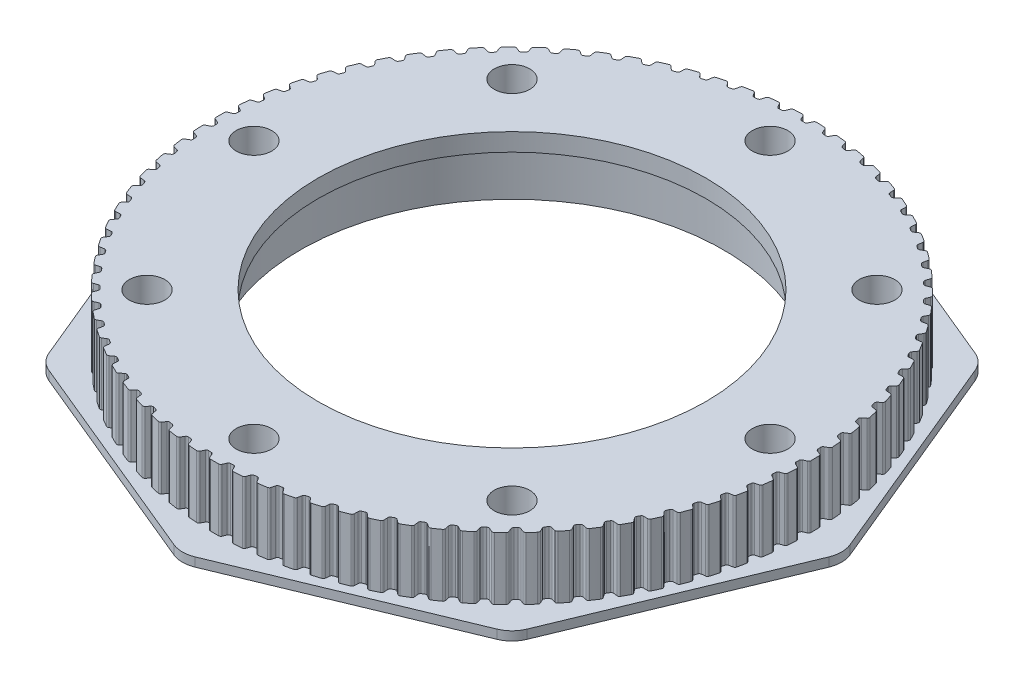
SolidWorks part; units mm, degrees
material "PVC rigide"
ref_plane "Plan de face" through (0, 0, 0) normal (0, 0, 1) x (1, 0, 0)
ref_plane "Plan de dessus" through (0, 0, 0) normal (0, 1, 0) x (1, 0, 0)
ref_plane "Plan de droite" through (0, 0, 0) normal (1, 0, 0) x (0, 0, -1)
sketch "Esquisse1" plane through (0, 0, 0) normal (0, 1, 0) x (1, 0, 0)
  line L0 (0, 0) -> (0, 74.5768) construction
  line L1 (-52.7338, 52.7338) -> (-74.5768, 0)
  line L2 (-74.5768, 0) -> (-52.7338, -52.7338)
  line L3 (-52.7338, -52.7338) -> (0, -74.5768)
  line L4 (0, -74.5768) -> (52.7338, -52.7338)
  line L5 (52.7338, -52.7338) -> (74.5768, 0)
  line L6 (74.5768, 0) -> (52.7338, 52.7338)
  line L7 (52.7338, 52.7338) -> (0, 74.5768)
  line L8 (0, 74.5768) -> (-52.7338, 52.7338)
  circle A1 centre (0, 0) radius 47.55
  circle A2 centre (0, 0) radius 68.9 construction
  dimension "D2" = 95.1
  dimension "D3" = 137.8
extrude "Boss.-Extru.1" add sketch "Esquisse1" along normal blind 16
fillet "Congé1" radius 6.2 8 edges at (0, 8, -74.5768) (52.7338, 8, -52.7338) (74.5768, 8, 0) (-52.7338, 8, 52.7338) (-74.5768, 8, 0) (-52.7338, 8, -52.7338) (52.7338, 8, 52.7338) (0, 8, 74.5768)
sketch "Esquisse2" plane through (0, 16, 0) normal (0, 1, 0) x (1, 0, 0)
  circle A0 centre (0, 0) radius 58 construction
  circle A1 centre (-58, 0) radius 3.1
  circle A2 centre (-41.0122, 41.0122) radius 3.1
  circle A3 centre (0, 58) radius 3.1
  circle A4 centre (41.0122, 41.0122) radius 3.1
  circle A5 centre (58, 0) radius 3.1
  circle A6 centre (41.0122, -41.0122) radius 3.1
  circle A7 centre (0, -58) radius 3.1
  circle A8 centre (-41.0122, -41.0122) radius 3.1
  dimension "D1" = 116
  dimension "D2" = 6.2
  dimension "D3" = 8
extrude "Enlèv. mat.-Extru.1" cut sketch "Esquisse2" against normal through all
sketch "Esquisse3" plane through (0, 16, 0) normal (0, 1, 0) x (1, 0, 0)
  circle A0 centre (-58, 0) radius 4
  circle A1 centre (-41.0122, 41.0122) radius 4
  circle A2 centre (0, 58) radius 4
  circle A3 centre (41.0122, 41.0122) radius 4
  circle A4 centre (58, 0) radius 4
  circle A5 centre (41.0122, -41.0122) radius 4
  circle A6 centre (0, -58) radius 4
  circle A7 centre (-41.0122, -41.0122) radius 4
  dimension "D1" = 8
  dimension "D2" = 8
extrude "Enlèv. mat.-Extru.2" cut sketch "Esquisse3" against normal blind 12.8
sketch "Esquisse5" plane through (0, 16, 0) normal (0, 1, 0) x (1, 0, 0)
  circle A0 centre (0, 0) radius 66.85
  dimension "D1" = 133.7
extrude "Enlèv. mat.-Extru.3" cut sketch "Esquisse5" against normal offset from surface (14 mm away) 2 flip side to cut up to face at (-58, 0, 3.1)
sketch "Esquisse6" plane through (0, 16, 0) normal (0, 1, 0) x (1, 0, 0)
  line L0 (0, 0) -> (0, 66.85) construction
  line L1 (-0.635, 65.45) -> (0.635, 65.45)
  line L2 (0.635, 65.45) -> (1.2821, 66.8377)
  line L3 (-0.635, 65.45) -> (-1.2821, 66.8377)
  line L4 (-1.2821, 66.8377) -> (1.2821, 66.8377) construction
  line L333 (-1.2821, 66.8377) -> (-1.2821, 67.3377)
  line L334 (-1.2821, 67.3377) -> (1.2821, 67.3377)
  line L335 (1.2821, 67.3377) -> (1.2821, 66.8377)
  line L336 (4.3167, 65.3106) -> (5.5831, 65.2145)
  line L337 (5.5831, 65.2145) -> (6.3333, 66.5493)
  line L338 (4.3167, 65.3106) -> (3.7764, 66.7432)
  line L339 (3.7764, 66.7432) -> (3.8142, 67.2418)
  line L340 (3.8142, 67.2418) -> (6.3711, 67.0479)
  line L341 (6.3711, 67.0479) -> (6.3333, 66.5493)
  line L342 (3.7764, 66.7432) -> (6.3333, 66.5493) construction
  line L343 (9.2437, 64.7971) -> (10.4992, 64.6055)
  line L344 (10.4992, 64.6055) -> (11.3482, 65.8797)
  line L345 (9.2437, 64.7971) -> (8.8133, 66.2665)
  line L346 (8.8133, 66.2665) -> (8.8887, 66.7608)
  line L347 (8.8887, 66.7608) -> (11.4236, 66.374)
  line L348 (11.4236, 66.374) -> (11.3482, 65.8797)
  line L349 (8.8133, 66.2665) -> (11.3482, 65.8797) construction
  line L350 (14.1178, 63.9124) -> (15.3552, 63.6264)
  line L351 (15.3552, 63.6264) -> (16.2981, 64.8328)
  line L352 (14.1178, 63.9124) -> (13.7997, 65.4102)
  line L353 (13.7997, 65.4102) -> (13.9123, 65.8973)
  line L354 (13.9123, 65.8973) -> (16.4107, 65.32)
  line L355 (16.4107, 65.32) -> (16.2981, 64.8328)
  line L356 (13.7997, 65.4102) -> (16.2981, 64.8328) construction
  line L357 (18.9109, 62.6616) -> (20.1232, 62.2829)
  line L358 (20.1232, 62.2829) -> (21.1546, 63.4145)
  line L359 (18.9109, 62.6616) -> (18.7071, 64.1792)
  line L360 (18.7071, 64.1792) -> (18.8562, 64.6564)
  line L361 (18.8562, 64.6564) -> (21.3037, 63.8918)
  line L362 (21.3037, 63.8918) -> (21.1546, 63.4145)
  line L363 (18.7071, 64.1792) -> (21.1546, 63.4145) construction
  line L364 (23.5958, 61.052) -> (24.7759, 60.5827)
  line L365 (24.7759, 60.5827) -> (25.89, 61.633)
  line L366 (23.5958, 61.052) -> (23.5073, 62.5806)
  line L367 (23.5073, 62.5806) -> (23.6921, 63.0452)
  line L368 (23.6921, 63.0452) -> (26.0748, 62.0976)
  line L369 (26.0748, 62.0976) -> (25.89, 61.633)
  line L370 (23.5073, 62.5806) -> (25.89, 61.633) construction
  line L371 (28.1455, 59.0926) -> (29.2867, 58.5354)
  line L372 (29.2867, 58.5354) -> (30.4771, 59.4985)
  line L373 (28.1455, 59.0926) -> (28.1729, 60.6235)
  line L374 (28.1729, 60.6235) -> (28.3923, 61.0728)
  line L375 (28.3923, 61.0728) -> (30.6965, 59.9478)
  line L376 (30.6965, 59.9478) -> (30.4771, 59.4985)
  line L377 (28.1729, 60.6235) -> (30.4771, 59.4985) construction
  line L378 (32.534, 56.7948) -> (33.6298, 56.1528)
  line L379 (33.6298, 56.1528) -> (34.8896, 57.0231)
  line L380 (32.534, 56.7948) -> (32.6771, 58.3192)
  line L381 (32.6771, 58.3192) -> (32.9298, 58.7506)
  line L382 (32.9298, 58.7506) -> (35.1423, 57.4546)
  line L383 (35.1423, 57.4546) -> (34.8896, 57.0231)
  line L384 (32.6771, 58.3192) -> (34.8896, 57.0231) construction
  line L385 (36.7361, 54.1716) -> (37.7803, 53.4486)
  line L386 (37.7803, 53.4486) -> (39.1023, 54.2212)
  line L387 (36.7361, 54.1716) -> (36.9941, 55.6809)
  line L388 (36.9941, 55.6809) -> (37.2787, 56.0919)
  line L389 (37.2787, 56.0919) -> (39.3869, 54.6322)
  line L390 (39.3869, 54.6322) -> (39.1023, 54.2212)
  line L391 (36.9941, 55.6809) -> (39.1023, 54.2212) construction
  line L392 (40.7279, 51.2381) -> (41.7143, 50.4383)
  line L393 (41.7143, 50.4383) -> (43.091, 51.1086)
  line L394 (40.7279, 51.2381) -> (41.0992, 52.7236)
  line L395 (41.0992, 52.7236) -> (41.4141, 53.112)
  line L396 (41.4141, 53.112) -> (43.4059, 51.497)
  line L397 (43.4059, 51.497) -> (43.091, 51.1086)
  line L398 (41.0992, 52.7236) -> (43.091, 51.1086) construction
  line L399 (44.4863, 48.0112) -> (45.4095, 47.139)
  line L400 (45.4095, 47.139) -> (46.8328, 47.7033)
  line L401 (44.4863, 48.0112) -> (44.9689, 49.4643)
  line L402 (44.9689, 49.4643) -> (45.3123, 49.8278)
  line L403 (45.3123, 49.8278) -> (47.1762, 48.0668)
  line L404 (47.1762, 48.0668) -> (46.8328, 47.7033)
  line L405 (44.9689, 49.4643) -> (46.8328, 47.7033) construction
  line L406 (47.9899, 44.5093) -> (48.8445, 43.5698)
  line L407 (48.8445, 43.5698) -> (50.3064, 44.0248)
  line L408 (47.9899, 44.5093) -> (48.5811, 45.9217)
  line L409 (48.5811, 45.9217) -> (48.9509, 46.2581)
  line L410 (48.9509, 46.2581) -> (50.6763, 44.3612)
  line L411 (50.6763, 44.3612) -> (50.3064, 44.0248)
  line L412 (48.5811, 45.9217) -> (50.3064, 44.0248) construction
  line L413 (51.2187, 40.7524) -> (51.9997, 39.7509)
  line L414 (51.9997, 39.7509) -> (53.4919, 40.0941)
  line L415 (51.2187, 40.7524) -> (51.9149, 42.1161)
  line L416 (51.9149, 42.1161) -> (52.3092, 42.4236)
  line L417 (52.3092, 42.4236) -> (53.8862, 40.4016)
  line L418 (53.8862, 40.4016) -> (53.4919, 40.0941)
  line L419 (51.9149, 42.1161) -> (53.4919, 40.0941) construction
  line L420 (54.154, 36.762) -> (54.8571, 35.7044)
  line L421 (54.8571, 35.7044) -> (56.371, 35.9338)
  line L422 (54.154, 36.762) -> (54.9514, 38.0692)
  line L423 (54.9514, 38.0692) -> (55.3678, 38.346)
  line L424 (55.3678, 38.346) -> (56.7874, 36.2106)
  line L425 (56.7874, 36.2106) -> (56.371, 35.9338)
  line L426 (54.9514, 38.0692) -> (56.371, 35.9338) construction
  line L427 (56.7792, 32.5612) -> (57.4003, 31.4534)
  line L428 (57.4003, 31.4534) -> (58.9272, 31.5676)
  line L429 (56.7792, 32.5612) -> (57.6732, 33.8042)
  line L430 (57.6732, 33.8042) -> (58.1093, 34.0488)
  line L431 (58.1093, 34.0488) -> (59.3633, 31.8121)
  line L432 (59.3633, 31.8121) -> (58.9272, 31.5676)
  line L433 (57.6732, 33.8042) -> (58.9272, 31.5676) construction
  line L434 (59.0791, 28.1738) -> (59.6147, 27.0222)
  line L435 (59.6147, 27.0222) -> (61.1458, 27.0206)
  line L436 (59.0791, 28.1738) -> (60.0646, 29.3457)
  line L437 (60.0646, 29.3457) -> (60.518, 29.5565)
  line L438 (60.518, 29.5565) -> (61.5992, 27.2314)
  line L439 (61.5992, 27.2314) -> (61.1458, 27.0206)
  line L440 (60.0646, 29.3457) -> (61.1458, 27.0206) construction
  line L441 (61.0407, 23.625) -> (61.4876, 22.4362)
  line L442 (61.4876, 22.4362) -> (63.0142, 22.3188)
  line L443 (61.0407, 23.625) -> (62.1119, 24.719)
  line L444 (62.1119, 24.719) -> (62.58, 24.895)
  line L445 (62.58, 24.895) -> (63.4822, 22.4948)
  line L446 (63.4822, 22.4948) -> (63.0142, 22.3188)
  line L447 (62.1119, 24.719) -> (63.0142, 22.3188) construction
  line L448 (62.6526, 18.9409) -> (63.0083, 17.7217)
  line L449 (63.0083, 17.7217) -> (64.5217, 17.4892)
  line L450 (62.6526, 18.9409) -> (63.8035, 19.9508)
  line L451 (63.8035, 19.9508) -> (64.2835, 20.0908)
  line L452 (64.2835, 20.0908) -> (65.0017, 17.6293)
  line L453 (65.0017, 17.6293) -> (64.5217, 17.4892)
  line L454 (63.8035, 19.9508) -> (64.5217, 17.4892) construction
  line L455 (63.9056, 14.1483) -> (64.1681, 12.9057)
  line L456 (64.1681, 12.9057) -> (65.6596, 12.5594)
  line L457 (63.9056, 14.1483) -> (65.1296, 15.0683)
  line L458 (65.1296, 15.0683) -> (65.6188, 15.1716)
  line L459 (65.6188, 15.1716) -> (66.1488, 12.6628)
  line L460 (66.1488, 12.6628) -> (65.6596, 12.5594)
  line L461 (65.1296, 15.0683) -> (65.6596, 12.5594) construction
  line L462 (64.7926, 9.2747) -> (64.9604, 8.0158)
  line L463 (64.9604, 8.0158) -> (66.4214, 7.5577)
  line L464 (64.7926, 9.2747) -> (66.0827, 10.0994)
  line L465 (66.0827, 10.0994) -> (66.5783, 10.1655)
  line L466 (66.5783, 10.1655) -> (66.917, 7.6238)
  line L467 (66.917, 7.6238) -> (66.4214, 7.5577)
  line L468 (66.0827, 10.0994) -> (66.4214, 7.5577) construction
  line L469 (65.3085, 4.348) -> (65.3806, 3.08)
  line L470 (65.3806, 3.08) -> (66.8028, 2.5127)
  line L471 (65.3085, 4.348) -> (66.6573, 5.0728)
  line L472 (66.6573, 5.0728) -> (67.1564, 5.1011)
  line L473 (67.1564, 5.1011) -> (67.302, 2.5411)
  line L474 (67.302, 2.5411) -> (66.8028, 2.5127)
  line L475 (66.6573, 5.0728) -> (66.8028, 2.5127) construction
  line L476 (65.4503, -0.6037) -> (65.4263, -1.8735)
  line L477 (65.4263, -1.8735) -> (66.8015, -2.5467)
  line L478 (65.4503, -0.6037) -> (66.85, 0.017)
  line L479 (66.85, 0.017) -> (67.3499, 0.0076)
  line L480 (67.3499, 0.0076) -> (67.3014, -2.5562)
  line L481 (67.3014, -2.5562) -> (66.8015, -2.5467)
  line L482 (66.85, 0.017) -> (66.8015, -2.5467) construction
  line L483 (65.2172, -5.5519) -> (65.0972, -6.8162)
  line L484 (65.0972, -6.8162) -> (66.4176, -7.5915)
  line L485 (65.2172, -5.5519) -> (66.6598, -5.0388)
  line L486 (66.6598, -5.0388) -> (67.1576, -5.0861)
  line L487 (67.1576, -5.0861) -> (66.9153, -7.6388)
  line L488 (66.9153, -7.6388) -> (66.4176, -7.5915)
  line L489 (66.6598, -5.0388) -> (66.4176, -7.5915) construction
  line L490 (64.6105, -10.4683) -> (64.3953, -11.7199)
  line L491 (64.3953, -11.7199) -> (65.6532, -12.5929)
  line L492 (64.6105, -10.4683) -> (66.0878, -10.0658)
  line L493 (66.0878, -10.0658) -> (66.5806, -10.1505)
  line L494 (66.5806, -10.1505) -> (66.146, -12.6776)
  line L495 (66.146, -12.6776) -> (65.6532, -12.5929)
  line L496 (66.0878, -10.0658) -> (65.6532, -12.5929) construction
  line L497 (63.6338, -15.3247) -> (63.3245, -16.5565)
  line L498 (63.3245, -16.5565) -> (64.5128, -17.5221)
  line L499 (63.6338, -15.3247) -> (65.1373, -15.0351)
  line L500 (65.1373, -15.0351) -> (65.6222, -15.1569)
  line L501 (65.6222, -15.1569) -> (64.9977, -17.6438)
  line L502 (64.9977, -17.6438) -> (64.5128, -17.5221)
  line L503 (65.1373, -15.0351) -> (64.5128, -17.5221) construction
  line L504 (62.2926, -20.0934) -> (61.891, -21.2982)
  line L505 (61.891, -21.2982) -> (63.0029, -22.3509)
  line L506 (62.2926, -20.0934) -> (63.8137, -19.9183)
  line L507 (63.8137, -19.9183) -> (64.288, -20.0764)
  line L508 (64.288, -20.0764) -> (63.4772, -22.509)
  line L509 (63.4772, -22.509) -> (63.0029, -22.3509)
  line L510 (63.8137, -19.9183) -> (63.0029, -22.3509) construction
  line L511 (60.5945, -24.7469) -> (60.103, -25.9179)
  line L512 (60.103, -25.9179) -> (61.132, -27.0517)
  line L513 (60.5945, -24.7469) -> (62.1245, -24.6874)
  line L514 (62.1245, -24.6874) -> (62.5855, -24.8809)
  line L515 (62.5855, -24.8809) -> (61.5931, -27.2452)
  line L516 (61.5931, -27.2452) -> (61.132, -27.0517)
  line L517 (62.1245, -24.6874) -> (61.132, -27.0517) construction
  line L518 (58.5494, -29.2587) -> (57.9707, -30.3892)
  line L519 (57.9707, -30.3892) -> (58.9111, -31.5976)
  line L520 (58.5494, -29.2587) -> (60.0795, -29.3151)
  line L521 (60.0795, -29.3151) -> (60.5246, -29.5429)
  line L522 (60.5246, -29.5429) -> (59.3561, -31.8254)
  line L523 (59.3561, -31.8254) -> (58.9111, -31.5976)
  line L524 (60.0795, -29.3151) -> (58.9111, -31.5976) construction
  line L525 (56.1689, -33.603) -> (55.5064, -34.6864)
  line L526 (55.5064, -34.6864) -> (56.3527, -35.9625)
  line L527 (56.1689, -33.603) -> (57.6904, -33.7749)
  line L528 (57.6904, -33.7749) -> (58.117, -34.0357)
  line L529 (58.117, -34.0357) -> (56.7792, -36.2233)
  line L530 (56.7792, -36.2233) -> (56.3527, -35.9625)
  line L531 (57.6904, -33.7749) -> (56.3527, -35.9625) construction
  line L532 (53.4667, -37.7547) -> (52.7241, -38.785)
  line L533 (52.7241, -38.785) -> (53.4715, -40.1214)
  line L534 (53.4667, -37.7547) -> (54.9708, -38.0412)
  line L535 (54.9708, -38.0412) -> (55.3764, -38.3335)
  line L536 (55.3764, -38.3335) -> (53.8771, -40.4137)
  line L537 (53.8771, -40.4137) -> (53.4715, -40.1214)
  line L538 (54.9708, -38.0412) -> (53.4715, -40.1214) construction
  line L539 (50.4582, -41.6902) -> (49.6398, -42.6614)
  line L540 (49.6398, -42.6614) -> (50.284, -44.0504)
  line L541 (50.4582, -41.6902) -> (51.9364, -42.0896)
  line L542 (51.9364, -42.0896) -> (52.3187, -42.4118)
  line L543 (52.3187, -42.4118) -> (50.6664, -44.3726)
  line L544 (50.6664, -44.3726) -> (50.284, -44.0504)
  line L545 (51.9364, -42.0896) -> (50.284, -44.0504) construction
  line L546 (47.1607, -45.3869) -> (46.2712, -46.2934)
  line L547 (46.2712, -46.2934) -> (46.8085, -47.7272)
  line L548 (47.1607, -45.3869) -> (48.6044, -45.897)
  line L549 (48.6044, -45.897) -> (48.9613, -46.2471)
  line L550 (48.9613, -46.2471) -> (47.1654, -48.0774)
  line L551 (47.1654, -48.0774) -> (46.8085, -47.7272)
  line L552 (48.6044, -45.897) -> (46.8085, -47.7272) construction
  line L553 (43.5931, -48.8236) -> (42.6376, -49.6602)
  line L554 (42.6376, -49.6602) -> (43.0649, -51.1306)
  line L555 (43.5931, -48.8236) -> (44.9941, -49.4414)
  line L556 (44.9941, -49.4414) -> (45.3235, -49.8176)
  line L557 (45.3235, -49.8176) -> (43.3943, -51.5067)
  line L558 (43.3943, -51.5067) -> (43.0649, -51.1306)
  line L559 (44.9941, -49.4414) -> (43.0649, -51.1306) construction
  line L560 (39.7758, -51.9807) -> (38.7598, -52.7426)
  line L561 (38.7598, -52.7426) -> (39.0746, -54.2411)
  line L562 (39.7758, -51.9807) -> (41.1261, -52.7026)
  line L563 (41.1261, -52.7026) -> (41.4261, -53.1027)
  line L564 (41.4261, -53.1027) -> (39.3746, -54.6411)
  line L565 (39.3746, -54.6411) -> (39.0746, -54.2411)
  line L566 (41.1261, -52.7026) -> (39.0746, -54.2411) construction
  line L567 (35.7306, -54.84) -> (34.6599, -55.5229)
  line L568 (34.6599, -55.5229) -> (34.8606, -57.0409)
  line L569 (35.7306, -54.84) -> (37.0224, -55.662)
  line L570 (37.0224, -55.662) -> (37.2913, -56.0836)
  line L571 (37.2913, -56.0836) -> (35.1294, -57.4625)
  line L572 (35.1294, -57.4625) -> (34.8606, -57.0409)
  line L573 (37.0224, -55.662) -> (34.8606, -57.0409) construction
  line L574 (31.4808, -57.3852) -> (30.3615, -57.9852)
  line L575 (30.3615, -57.9852) -> (30.4468, -59.514)
  line L576 (31.4808, -57.3852) -> (32.7068, -58.3026)
  line L577 (32.7068, -58.3026) -> (32.943, -58.7433)
  line L578 (32.943, -58.7433) -> (30.683, -59.9547)
  line L579 (30.683, -59.9547) -> (30.4468, -59.514)
  line L580 (32.7068, -58.3026) -> (30.4468, -59.514) construction
  line L581 (27.0507, -59.6017) -> (25.8892, -60.1153)
  line L582 (25.8892, -60.1153) -> (25.8586, -61.6462)
  line L583 (27.0507, -59.6017) -> (28.2037, -60.6092)
  line L584 (28.2037, -60.6092) -> (28.406, -61.0665)
  line L585 (28.406, -61.0665) -> (26.0608, -62.1035)
  line L586 (26.0608, -62.1035) -> (25.8586, -61.6462)
  line L587 (28.2037, -60.6092) -> (25.8586, -61.6462) construction
  line L588 (22.4656, -61.4768) -> (21.2686, -61.9011)
  line L589 (21.2686, -61.9011) -> (21.1223, -63.4253)
  line L590 (22.4656, -61.4768) -> (23.5392, -62.5686)
  line L591 (23.5392, -62.5686) -> (23.7062, -63.0399)
  line L592 (23.7062, -63.0399) -> (21.2894, -63.8966)
  line L593 (21.2894, -63.8966) -> (21.1223, -63.4253)
  line L594 (23.5392, -62.5686) -> (21.1223, -63.4253) construction
  line L595 (17.7519, -62.9998) -> (16.5262, -63.3324)
  line L596 (16.5262, -63.3324) -> (16.2651, -64.8411)
  line L597 (17.7519, -62.9998) -> (18.7398, -64.1696)
  line L598 (18.7398, -64.1696) -> (18.8707, -64.6522)
  line L599 (18.8707, -64.6522) -> (16.396, -65.3237)
  line L600 (16.396, -65.3237) -> (16.2651, -64.8411)
  line L601 (18.7398, -64.1696) -> (16.2651, -64.8411) construction
  line L602 (12.9364, -64.1619) -> (11.6891, -64.4009)
  line L603 (11.6891, -64.4009) -> (11.3146, -65.8855)
  line L604 (12.9364, -64.1619) -> (13.833, -65.4031)
  line L605 (13.833, -65.4031) -> (13.9271, -65.8942)
  line L606 (13.9271, -65.8942) -> (11.4087, -66.3766)
  line L607 (11.4087, -66.3766) -> (11.3146, -65.8855)
  line L608 (13.833, -65.4031) -> (11.3146, -65.8855) construction
  line L609 (8.0469, -64.9565) -> (6.7851, -65.1004)
  line L610 (6.7851, -65.1004) -> (6.2994, -66.5525)
  line L611 (8.0469, -64.9565) -> (8.8471, -66.262)
  line L612 (8.8471, -66.262) -> (8.9037, -66.7588)
  line L613 (8.9037, -66.7588) -> (6.356, -67.0493)
  line L614 (6.356, -67.0493) -> (6.2994, -66.5525)
  line L615 (8.8471, -66.262) -> (6.2994, -66.5525) construction
  line L616 (3.1113, -65.3791) -> (1.8422, -65.4272)
  line L617 (1.8422, -65.4272) -> (1.2481, -66.8383)
  line L618 (3.1113, -65.3791) -> (3.8104, -66.7413)
  line L619 (3.8104, -66.7413) -> (3.8293, -67.241)
  line L620 (3.8293, -67.241) -> (1.267, -67.338)
  line L621 (1.267, -67.338) -> (1.2481, -66.8383)
  line L622 (3.8104, -66.7413) -> (1.2481, -66.8383) construction
  line L623 (-1.8422, -65.4272) -> (-3.1113, -65.3791)
  line L624 (-3.1113, -65.3791) -> (-3.8104, -66.7413)
  line L625 (-1.8422, -65.4272) -> (-1.2481, -66.8383)
  line L626 (-1.2481, -66.8383) -> (-1.267, -67.338)
  line L627 (-1.267, -67.338) -> (-3.8293, -67.241)
  line L628 (-3.8293, -67.241) -> (-3.8104, -66.7413)
  line L629 (-1.2481, -66.8383) -> (-3.8104, -66.7413) construction
  line L630 (-6.7851, -65.1004) -> (-8.0469, -64.9565)
  line L631 (-8.0469, -64.9565) -> (-8.8471, -66.262)
  line L632 (-6.7851, -65.1004) -> (-6.2994, -66.5525)
  line L633 (-6.2994, -66.5525) -> (-6.356, -67.0493)
  line L634 (-6.356, -67.0493) -> (-8.9037, -66.7588)
  line L635 (-8.9037, -66.7588) -> (-8.8471, -66.262)
  line L636 (-6.2994, -66.5525) -> (-8.8471, -66.262) construction
  line L637 (-11.6891, -64.4009) -> (-12.9364, -64.1619)
  line L638 (-12.9364, -64.1619) -> (-13.833, -65.4031)
  line L639 (-11.6891, -64.4009) -> (-11.3146, -65.8855)
  line L640 (-11.3146, -65.8855) -> (-11.4087, -66.3766)
  line L641 (-11.4087, -66.3766) -> (-13.9271, -65.8942)
  line L642 (-13.9271, -65.8942) -> (-13.833, -65.4031)
  line L643 (-11.3146, -65.8855) -> (-13.833, -65.4031) construction
  line L644 (-16.5262, -63.3324) -> (-17.7519, -62.9998)
  line L645 (-17.7519, -62.9998) -> (-18.7398, -64.1696)
  line L646 (-16.5262, -63.3324) -> (-16.2651, -64.8411)
  line L647 (-16.2651, -64.8411) -> (-16.396, -65.3237)
  line L648 (-16.396, -65.3237) -> (-18.8707, -64.6522)
  line L649 (-18.8707, -64.6522) -> (-18.7398, -64.1696)
  line L650 (-16.2651, -64.8411) -> (-18.7398, -64.1696) construction
  line L651 (-21.2686, -61.9011) -> (-22.4656, -61.4768)
  line L652 (-22.4656, -61.4768) -> (-23.5392, -62.5686)
  line L653 (-21.2686, -61.9011) -> (-21.1223, -63.4253)
  line L654 (-21.1223, -63.4253) -> (-21.2894, -63.8966)
  line L655 (-21.2894, -63.8966) -> (-23.7062, -63.0399)
  line L656 (-23.7062, -63.0399) -> (-23.5392, -62.5686)
  line L657 (-21.1223, -63.4253) -> (-23.5392, -62.5686) construction
  line L658 (-25.8892, -60.1153) -> (-27.0507, -59.6017)
  line L659 (-27.0507, -59.6017) -> (-28.2037, -60.6092)
  line L660 (-25.8892, -60.1153) -> (-25.8586, -61.6462)
  line L661 (-25.8586, -61.6462) -> (-26.0608, -62.1035)
  line L662 (-26.0608, -62.1035) -> (-28.406, -61.0665)
  line L663 (-28.406, -61.0665) -> (-28.2037, -60.6092)
  line L664 (-25.8586, -61.6462) -> (-28.2037, -60.6092) construction
  line L665 (-30.3615, -57.9852) -> (-31.4808, -57.3852)
  line L666 (-31.4808, -57.3852) -> (-32.7068, -58.3026)
  line L667 (-30.3615, -57.9852) -> (-30.4468, -59.514)
  line L668 (-30.4468, -59.514) -> (-30.683, -59.9547)
  line L669 (-30.683, -59.9547) -> (-32.943, -58.7433)
  line L670 (-32.943, -58.7433) -> (-32.7068, -58.3026)
  line L671 (-30.4468, -59.514) -> (-32.7068, -58.3026) construction
  line L672 (-34.6599, -55.5229) -> (-35.7306, -54.84)
  line L673 (-35.7306, -54.84) -> (-37.0224, -55.662)
  line L674 (-34.6599, -55.5229) -> (-34.8606, -57.0409)
  line L675 (-34.8606, -57.0409) -> (-35.1294, -57.4625)
  line L676 (-35.1294, -57.4625) -> (-37.2913, -56.0836)
  line L677 (-37.2913, -56.0836) -> (-37.0224, -55.662)
  line L678 (-34.8606, -57.0409) -> (-37.0224, -55.662) construction
  line L679 (-38.7598, -52.7426) -> (-39.7758, -51.9807)
  line L680 (-39.7758, -51.9807) -> (-41.1261, -52.7026)
  line L681 (-38.7598, -52.7426) -> (-39.0746, -54.2411)
  line L682 (-39.0746, -54.2411) -> (-39.3746, -54.6411)
  line L683 (-39.3746, -54.6411) -> (-41.4261, -53.1027)
  line L684 (-41.4261, -53.1027) -> (-41.1261, -52.7026)
  line L685 (-39.0746, -54.2411) -> (-41.1261, -52.7026) construction
  line L686 (-42.6376, -49.6602) -> (-43.5931, -48.8236)
  line L687 (-43.5931, -48.8236) -> (-44.9941, -49.4414)
  line L688 (-42.6376, -49.6602) -> (-43.0649, -51.1306)
  line L689 (-43.0649, -51.1306) -> (-43.3943, -51.5067)
  line L690 (-43.3943, -51.5067) -> (-45.3235, -49.8176)
  line L691 (-45.3235, -49.8176) -> (-44.9941, -49.4414)
  line L692 (-43.0649, -51.1306) -> (-44.9941, -49.4414) construction
  line L693 (-46.2712, -46.2934) -> (-47.1607, -45.3869)
  line L694 (-47.1607, -45.3869) -> (-48.6044, -45.897)
  line L695 (-46.2712, -46.2934) -> (-46.8085, -47.7272)
  line L696 (-46.8085, -47.7272) -> (-47.1654, -48.0774)
  line L697 (-47.1654, -48.0774) -> (-48.9613, -46.2471)
  line L698 (-48.9613, -46.2471) -> (-48.6044, -45.897)
  line L699 (-46.8085, -47.7272) -> (-48.6044, -45.897) construction
  line L700 (-49.6398, -42.6614) -> (-50.4582, -41.6902)
  line L701 (-50.4582, -41.6902) -> (-51.9364, -42.0896)
  line L702 (-49.6398, -42.6614) -> (-50.284, -44.0504)
  line L703 (-50.284, -44.0504) -> (-50.6664, -44.3726)
  line L704 (-50.6664, -44.3726) -> (-52.3187, -42.4118)
  line L705 (-52.3187, -42.4118) -> (-51.9364, -42.0896)
  line L706 (-50.284, -44.0504) -> (-51.9364, -42.0896) construction
  line L707 (-52.7241, -38.785) -> (-53.4667, -37.7547)
  line L708 (-53.4667, -37.7547) -> (-54.9708, -38.0412)
  line L709 (-52.7241, -38.785) -> (-53.4715, -40.1214)
  line L710 (-53.4715, -40.1214) -> (-53.8771, -40.4137)
  line L711 (-53.8771, -40.4137) -> (-55.3764, -38.3335)
  line L712 (-55.3764, -38.3335) -> (-54.9708, -38.0412)
  line L713 (-53.4715, -40.1214) -> (-54.9708, -38.0412) construction
  line L714 (-55.5064, -34.6864) -> (-56.1689, -33.603)
  line L715 (-56.1689, -33.603) -> (-57.6904, -33.7749)
  line L716 (-55.5064, -34.6864) -> (-56.3527, -35.9625)
  line L717 (-56.3527, -35.9625) -> (-56.7792, -36.2233)
  line L718 (-56.7792, -36.2233) -> (-58.117, -34.0357)
  line L719 (-58.117, -34.0357) -> (-57.6904, -33.7749)
  line L720 (-56.3527, -35.9625) -> (-57.6904, -33.7749) construction
  line L721 (-57.9707, -30.3892) -> (-58.5494, -29.2587)
  line L722 (-58.5494, -29.2587) -> (-60.0795, -29.3151)
  line L723 (-57.9707, -30.3892) -> (-58.9111, -31.5976)
  line L724 (-58.9111, -31.5976) -> (-59.3561, -31.8254)
  line L725 (-59.3561, -31.8254) -> (-60.5246, -29.5429)
  line L726 (-60.5246, -29.5429) -> (-60.0795, -29.3151)
  line L727 (-58.9111, -31.5976) -> (-60.0795, -29.3151) construction
  line L728 (-60.103, -25.9179) -> (-60.5945, -24.7469)
  line L729 (-60.5945, -24.7469) -> (-62.1245, -24.6874)
  line L730 (-60.103, -25.9179) -> (-61.132, -27.0517)
  line L731 (-61.132, -27.0517) -> (-61.5931, -27.2452)
  line L732 (-61.5931, -27.2452) -> (-62.5855, -24.8809)
  line L733 (-62.5855, -24.8809) -> (-62.1245, -24.6874)
  line L734 (-61.132, -27.0517) -> (-62.1245, -24.6874) construction
  line L735 (-61.891, -21.2982) -> (-62.2926, -20.0934)
  line L736 (-62.2926, -20.0934) -> (-63.8137, -19.9183)
  line L737 (-61.891, -21.2982) -> (-63.0029, -22.3509)
  line L738 (-63.0029, -22.3509) -> (-63.4772, -22.509)
  line L739 (-63.4772, -22.509) -> (-64.288, -20.0764)
  line L740 (-64.288, -20.0764) -> (-63.8137, -19.9183)
  line L741 (-63.0029, -22.3509) -> (-63.8137, -19.9183) construction
  line L742 (-63.3245, -16.5565) -> (-63.6338, -15.3247)
  line L743 (-63.6338, -15.3247) -> (-65.1373, -15.0351)
  line L744 (-63.3245, -16.5565) -> (-64.5128, -17.5221)
  line L745 (-64.5128, -17.5221) -> (-64.9977, -17.6438)
  line L746 (-64.9977, -17.6438) -> (-65.6222, -15.1569)
  line L747 (-65.6222, -15.1569) -> (-65.1373, -15.0351)
  line L748 (-64.5128, -17.5221) -> (-65.1373, -15.0351) construction
  line L749 (-64.3953, -11.7199) -> (-64.6105, -10.4683)
  line L750 (-64.6105, -10.4683) -> (-66.0878, -10.0658)
  line L751 (-64.3953, -11.7199) -> (-65.6532, -12.5929)
  line L752 (-65.6532, -12.5929) -> (-66.146, -12.6776)
  line L753 (-66.146, -12.6776) -> (-66.5806, -10.1505)
  line L754 (-66.5806, -10.1505) -> (-66.0878, -10.0658)
  line L755 (-65.6532, -12.5929) -> (-66.0878, -10.0658) construction
  line L756 (-65.0972, -6.8162) -> (-65.2172, -5.5519)
  line L757 (-65.2172, -5.5519) -> (-66.6598, -5.0388)
  line L758 (-65.0972, -6.8162) -> (-66.4176, -7.5915)
  line L759 (-66.4176, -7.5915) -> (-66.9153, -7.6388)
  line L760 (-66.9153, -7.6388) -> (-67.1576, -5.0861)
  line L761 (-67.1576, -5.0861) -> (-66.6598, -5.0388)
  line L762 (-66.4176, -7.5915) -> (-66.6598, -5.0388) construction
  line L763 (-65.4263, -1.8735) -> (-65.4503, -0.6037)
  line L764 (-65.4503, -0.6037) -> (-66.85, 0.017)
  line L765 (-65.4263, -1.8735) -> (-66.8015, -2.5467)
  line L766 (-66.8015, -2.5467) -> (-67.3014, -2.5562)
  line L767 (-67.3014, -2.5562) -> (-67.3499, 0.0076)
  line L768 (-67.3499, 0.0076) -> (-66.85, 0.017)
  line L769 (-66.8015, -2.5467) -> (-66.85, 0.017) construction
  line L770 (-65.3806, 3.08) -> (-65.3085, 4.348)
  line L771 (-65.3085, 4.348) -> (-66.6573, 5.0728)
  line L772 (-65.3806, 3.08) -> (-66.8028, 2.5127)
  line L773 (-66.8028, 2.5127) -> (-67.302, 2.5411)
  line L774 (-67.302, 2.5411) -> (-67.1564, 5.1011)
  line L775 (-67.1564, 5.1011) -> (-66.6573, 5.0728)
  line L776 (-66.8028, 2.5127) -> (-66.6573, 5.0728) construction
  line L777 (-64.9604, 8.0158) -> (-64.7926, 9.2747)
  line L778 (-64.7926, 9.2747) -> (-66.0827, 10.0994)
  line L779 (-64.9604, 8.0158) -> (-66.4214, 7.5577)
  line L780 (-66.4214, 7.5577) -> (-66.917, 7.6238)
  line L781 (-66.917, 7.6238) -> (-66.5783, 10.1655)
  line L782 (-66.5783, 10.1655) -> (-66.0827, 10.0994)
  line L783 (-66.4214, 7.5577) -> (-66.0827, 10.0994) construction
  line L784 (-64.1681, 12.9057) -> (-63.9056, 14.1483)
  line L785 (-63.9056, 14.1483) -> (-65.1296, 15.0683)
  line L786 (-64.1681, 12.9057) -> (-65.6596, 12.5594)
  line L787 (-65.6596, 12.5594) -> (-66.1488, 12.6628)
  line L788 (-66.1488, 12.6628) -> (-65.6188, 15.1716)
  line L789 (-65.6188, 15.1716) -> (-65.1296, 15.0683)
  line L790 (-65.6596, 12.5594) -> (-65.1296, 15.0683) construction
  line L791 (-63.0083, 17.7217) -> (-62.6526, 18.9409)
  line L792 (-62.6526, 18.9409) -> (-63.8035, 19.9508)
  line L793 (-63.0083, 17.7217) -> (-64.5217, 17.4892)
  line L794 (-64.5217, 17.4892) -> (-65.0017, 17.6293)
  line L795 (-65.0017, 17.6293) -> (-64.2835, 20.0908)
  line L796 (-64.2835, 20.0908) -> (-63.8035, 19.9508)
  line L797 (-64.5217, 17.4892) -> (-63.8035, 19.9508) construction
  line L798 (-61.4876, 22.4362) -> (-61.0407, 23.625)
  line L799 (-61.0407, 23.625) -> (-62.1119, 24.719)
  line L800 (-61.4876, 22.4362) -> (-63.0142, 22.3188)
  line L801 (-63.0142, 22.3188) -> (-63.4822, 22.4948)
  line L802 (-63.4822, 22.4948) -> (-62.58, 24.895)
  line L803 (-62.58, 24.895) -> (-62.1119, 24.719)
  line L804 (-63.0142, 22.3188) -> (-62.1119, 24.719) construction
  line L805 (-59.6147, 27.0222) -> (-59.0791, 28.1738)
  line L806 (-59.0791, 28.1738) -> (-60.0646, 29.3457)
  line L807 (-59.6147, 27.0222) -> (-61.1458, 27.0206)
  line L808 (-61.1458, 27.0206) -> (-61.5992, 27.2314)
  line L809 (-61.5992, 27.2314) -> (-60.518, 29.5565)
  line L810 (-60.518, 29.5565) -> (-60.0646, 29.3457)
  line L811 (-61.1458, 27.0206) -> (-60.0646, 29.3457) construction
  line L812 (-57.4003, 31.4534) -> (-56.7792, 32.5612)
  line L813 (-56.7792, 32.5612) -> (-57.6732, 33.8042)
  line L814 (-57.4003, 31.4534) -> (-58.9272, 31.5676)
  line L815 (-58.9272, 31.5676) -> (-59.3633, 31.8121)
  line L816 (-59.3633, 31.8121) -> (-58.1093, 34.0488)
  line L817 (-58.1093, 34.0488) -> (-57.6732, 33.8042)
  line L818 (-58.9272, 31.5676) -> (-57.6732, 33.8042) construction
  line L819 (-54.8571, 35.7044) -> (-54.154, 36.762)
  line L820 (-54.154, 36.762) -> (-54.9514, 38.0692)
  line L821 (-54.8571, 35.7044) -> (-56.371, 35.9338)
  line L822 (-56.371, 35.9338) -> (-56.7874, 36.2106)
  line L823 (-56.7874, 36.2106) -> (-55.3678, 38.346)
  line L824 (-55.3678, 38.346) -> (-54.9514, 38.0692)
  line L825 (-56.371, 35.9338) -> (-54.9514, 38.0692) construction
  line L826 (-51.9997, 39.7509) -> (-51.2187, 40.7524)
  line L827 (-51.2187, 40.7524) -> (-51.9149, 42.1161)
  line L828 (-51.9997, 39.7509) -> (-53.4919, 40.0941)
  line L829 (-53.4919, 40.0941) -> (-53.8862, 40.4016)
  line L830 (-53.8862, 40.4016) -> (-52.3092, 42.4236)
  line L831 (-52.3092, 42.4236) -> (-51.9149, 42.1161)
  line L832 (-53.4919, 40.0941) -> (-51.9149, 42.1161) construction
  line L833 (-48.8445, 43.5698) -> (-47.9899, 44.5093)
  line L834 (-47.9899, 44.5093) -> (-48.5811, 45.9217)
  line L835 (-48.8445, 43.5698) -> (-50.3064, 44.0248)
  line L836 (-50.3064, 44.0248) -> (-50.6763, 44.3612)
  line L837 (-50.6763, 44.3612) -> (-48.9509, 46.2581)
  line L838 (-48.9509, 46.2581) -> (-48.5811, 45.9217)
  line L839 (-50.3064, 44.0248) -> (-48.5811, 45.9217) construction
  line L840 (-45.4095, 47.139) -> (-44.4863, 48.0112)
  line L841 (-44.4863, 48.0112) -> (-44.9689, 49.4643)
  line L842 (-45.4095, 47.139) -> (-46.8328, 47.7033)
  line L843 (-46.8328, 47.7033) -> (-47.1762, 48.0668)
  line L844 (-47.1762, 48.0668) -> (-45.3123, 49.8278)
  line L845 (-45.3123, 49.8278) -> (-44.9689, 49.4643)
  line L846 (-46.8328, 47.7033) -> (-44.9689, 49.4643) construction
  line L847 (-41.7143, 50.4383) -> (-40.7279, 51.2381)
  line L848 (-40.7279, 51.2381) -> (-41.0992, 52.7236)
  line L849 (-41.7143, 50.4383) -> (-43.091, 51.1086)
  line L850 (-43.091, 51.1086) -> (-43.4059, 51.497)
  line L851 (-43.4059, 51.497) -> (-41.4141, 53.112)
  line L852 (-41.4141, 53.112) -> (-41.0992, 52.7236)
  line L853 (-43.091, 51.1086) -> (-41.0992, 52.7236) construction
  line L854 (-37.7803, 53.4486) -> (-36.7361, 54.1716)
  line L855 (-36.7361, 54.1716) -> (-36.9941, 55.6809)
  line L856 (-37.7803, 53.4486) -> (-39.1023, 54.2212)
  line L857 (-39.1023, 54.2212) -> (-39.3869, 54.6322)
  line L858 (-39.3869, 54.6322) -> (-37.2787, 56.0919)
  line L859 (-37.2787, 56.0919) -> (-36.9941, 55.6809)
  line L860 (-39.1023, 54.2212) -> (-36.9941, 55.6809) construction
  line L861 (-33.6298, 56.1528) -> (-32.534, 56.7948)
  line L862 (-32.534, 56.7948) -> (-32.6771, 58.3192)
  line L863 (-33.6298, 56.1528) -> (-34.8896, 57.0231)
  line L864 (-34.8896, 57.0231) -> (-35.1423, 57.4546)
  line L865 (-35.1423, 57.4546) -> (-32.9298, 58.7506)
  line L866 (-32.9298, 58.7506) -> (-32.6771, 58.3192)
  line L867 (-34.8896, 57.0231) -> (-32.6771, 58.3192) construction
  line L868 (-29.2867, 58.5354) -> (-28.1455, 59.0926)
  line L869 (-28.1455, 59.0926) -> (-28.1729, 60.6235)
  line L870 (-29.2867, 58.5354) -> (-30.4771, 59.4985)
  line L871 (-30.4771, 59.4985) -> (-30.6965, 59.9478)
  line L872 (-30.6965, 59.9478) -> (-28.3923, 61.0728)
  line L873 (-28.3923, 61.0728) -> (-28.1729, 60.6235)
  line L874 (-30.4771, 59.4985) -> (-28.1729, 60.6235) construction
  line L875 (-24.7759, 60.5827) -> (-23.5958, 61.052)
  line L876 (-23.5958, 61.052) -> (-23.5073, 62.5806)
  line L877 (-24.7759, 60.5827) -> (-25.89, 61.633)
  line L878 (-25.89, 61.633) -> (-26.0748, 62.0976)
  line L879 (-26.0748, 62.0976) -> (-23.6921, 63.0452)
  line L880 (-23.6921, 63.0452) -> (-23.5073, 62.5806)
  line L881 (-25.89, 61.633) -> (-23.5073, 62.5806) construction
  line L882 (-20.1232, 62.2829) -> (-18.9109, 62.6616)
  line L883 (-18.9109, 62.6616) -> (-18.7071, 64.1792)
  line L884 (-20.1232, 62.2829) -> (-21.1546, 63.4145)
  line L885 (-21.1546, 63.4145) -> (-21.3037, 63.8918)
  line L886 (-21.3037, 63.8918) -> (-18.8562, 64.6564)
  line L887 (-18.8562, 64.6564) -> (-18.7071, 64.1792)
  line L888 (-21.1546, 63.4145) -> (-18.7071, 64.1792) construction
  line L889 (-15.3552, 63.6264) -> (-14.1178, 63.9124)
  line L890 (-14.1178, 63.9124) -> (-13.7997, 65.4102)
  line L891 (-15.3552, 63.6264) -> (-16.2981, 64.8328)
  line L892 (-16.2981, 64.8328) -> (-16.4107, 65.32)
  line L893 (-16.4107, 65.32) -> (-13.9123, 65.8973)
  line L894 (-13.9123, 65.8973) -> (-13.7997, 65.4102)
  line L895 (-16.2981, 64.8328) -> (-13.7997, 65.4102) construction
  line L896 (-10.4992, 64.6055) -> (-9.2437, 64.7971)
  line L897 (-9.2437, 64.7971) -> (-8.8133, 66.2665)
  line L898 (-10.4992, 64.6055) -> (-11.3482, 65.8797)
  line L899 (-11.3482, 65.8797) -> (-11.4236, 66.374)
  line L900 (-11.4236, 66.374) -> (-8.8887, 66.7608)
  line L901 (-8.8887, 66.7608) -> (-8.8133, 66.2665)
  line L902 (-11.3482, 65.8797) -> (-8.8133, 66.2665) construction
  line L903 (-5.5831, 65.2145) -> (-4.3167, 65.3106)
  line L904 (-4.3167, 65.3106) -> (-3.7764, 66.7432)
  line L905 (-5.5831, 65.2145) -> (-6.3333, 66.5493)
  line L906 (-6.3333, 66.5493) -> (-6.3711, 67.0479)
  line L907 (-6.3711, 67.0479) -> (-3.8142, 67.2418)
  line L908 (-3.8142, 67.2418) -> (-3.7764, 66.7432)
  line L909 (-6.3333, 66.5493) -> (-3.7764, 66.7432) construction
  circle A0 centre (0, 0) radius 66.85 construction
  point P11 (0, 65.45)
  point P21 (4.9499, 65.2626)
  point P28 (9.8715, 64.7013)
  point P35 (14.7365, 63.7694)
  point P42 (19.5171, 62.4723)
  point P49 (24.1859, 60.8173)
  point P56 (28.7161, 58.814)
  point P63 (33.0819, 56.4738)
  point P70 (37.2582, 53.8101)
  point P77 (41.2211, 50.8382)
  point P84 (44.9479, 47.5751)
  point P91 (48.4172, 44.0395)
  point P98 (51.6092, 40.2516)
  point P105 (54.5056, 36.2332)
  point P112 (57.0897, 32.0073)
  point P119 (59.3469, 27.598)
  point P126 (61.2641, 23.0306)
  point P133 (62.8304, 18.3313)
  point P140 (64.0369, 13.527)
  point P147 (64.8765, 8.6453)
  point P154 (65.3445, 3.714)
  point P161 (65.4383, -1.2386)
  point P168 (65.1572, -6.1841)
  point P175 (64.5029, -11.0941)
  point P182 (63.4791, -15.9406)
  point P189 (62.0918, -20.6958)
  point P196 (60.3487, -25.3324)
  point P203 (58.26, -29.824)
  point P210 (55.8376, -34.1447)
  point P217 (53.0954, -38.2699)
  point P224 (50.049, -42.1758)
  point P231 (46.716, -45.8401)
  point P238 (43.1154, -49.2419)
  point P245 (39.2678, -52.3617)
  point P252 (35.1953, -55.1815)
  point P259 (30.9212, -57.6852)
  point P266 (26.47, -59.8585)
  point P273 (21.8671, -61.689)
  point P280 (17.139, -63.1661)
  point P287 (12.3128, -64.2814)
  point P294 (7.416, -65.0285)
  point P301 (2.4767, -65.4031)
  point P308 (-2.4767, -65.4031)
  point P315 (-7.416, -65.0285)
  point P322 (-12.3128, -64.2814)
  point P329 (-17.139, -63.1661)
  point P336 (-21.8671, -61.689)
  point P343 (-26.47, -59.8585)
  point P350 (-30.9212, -57.6852)
  point P357 (-35.1953, -55.1815)
  point P364 (-39.2678, -52.3617)
  point P371 (-43.1154, -49.2419)
  point P378 (-46.716, -45.8401)
  point P385 (-50.049, -42.1758)
  point P392 (-53.0954, -38.2699)
  point P399 (-55.8376, -34.1447)
  point P406 (-58.26, -29.824)
  point P413 (-60.3487, -25.3324)
  point P420 (-62.0918, -20.6958)
  point P427 (-63.4791, -15.9406)
  point P434 (-64.5029, -11.0941)
  point P441 (-65.1572, -6.1841)
  point P448 (-65.4383, -1.2386)
  point P455 (-65.3445, 3.714)
  point P462 (-64.8765, 8.6453)
  point P469 (-64.0369, 13.527)
  point P476 (-62.8304, 18.3313)
  point P483 (-61.2641, 23.0306)
  point P490 (-59.3469, 27.598)
  point P497 (-57.0897, 32.0073)
  point P504 (-54.5056, 36.2332)
  point P511 (-51.6092, 40.2516)
  point P518 (-48.4172, 44.0395)
  point P525 (-44.9479, 47.5751)
  point P532 (-41.2211, 50.8382)
  point P539 (-37.2582, 53.8101)
  point P546 (-33.0819, 56.4738)
  point P553 (-28.7161, 58.814)
  point P560 (-24.1859, 60.8173)
  point P567 (-19.5171, 62.4723)
  point P574 (-14.7365, 63.7694)
  point P581 (-9.8715, 64.7013)
  point P588 (-4.9499, 65.2626)
  dimension "D1" = 1.27
  dimension "D2" = 25
  dimension "D3" = 1.4
  dimension "D5" = 0.5
  dimension "D4" = 83
extrude "Enlèv. mat.-Extru.6" cut sketch "Esquisse6" against normal up to surface (14 mm away) up to face at (0, 2, 0)
fillet "Congé2" radius 0.508 34 edges at (-65.3806, 9, -3.08) (-66.0878, 9, 10.0658) (-61.891, 9, 21.2982) (-63.0029, 9, 22.3509) (-62.1245, 9, 24.6874) (-52.7241, 9, 38.785) (-34.8606, 9, 57.0409) (-30.4468, 9, 59.514) (-25.8586, 9, 61.6462) (-18.7398, 9, 64.1696) (-12.9364, 9, 64.1619) (-11.6891, 9, 64.4009) (-8.8471, 9, 66.262) (3.8104, 9, 66.7413) (13.833, 9, 65.4031) (22.4656, 9, 61.4768) (31.4808, 9, 57.3852) (35.7306, 9, 54.84) (50.4582, 9, 41.6902) (64.6105, 9, 10.4683) (65.0972, 9, 6.8162) (65.4503, 9, 0.6037) (66.6573, 9, -5.0728) (62.1119, 9, -24.719) (59.0791, 9, -28.1738) (48.8445, 9, -43.5698) (18.9109, 9, -62.6616) (9.2437, 9, -64.7971) (-8.8133, 9, -66.2665) (-15.3552, 9, -63.6264) (-48.5811, 9, -45.9217) (-54.154, 9, -36.762) (-59.0791, 9, -28.1738) (-61.4876, 9, -22.4362)
sketch "Esquisse7" plane through (0, 16, 0) normal (0, 1, 0) x (1, 0, 0)
  circle A0 centre (0, 0) radius 47.55 construction
  circle A1 centre (0, 0) radius 47.55
  circle A2 centre (0, 0) radius 43.55
  dimension "D1" = 4
extrude "Boss.-Extru.2" add sketch "Esquisse7" against normal blind 4
